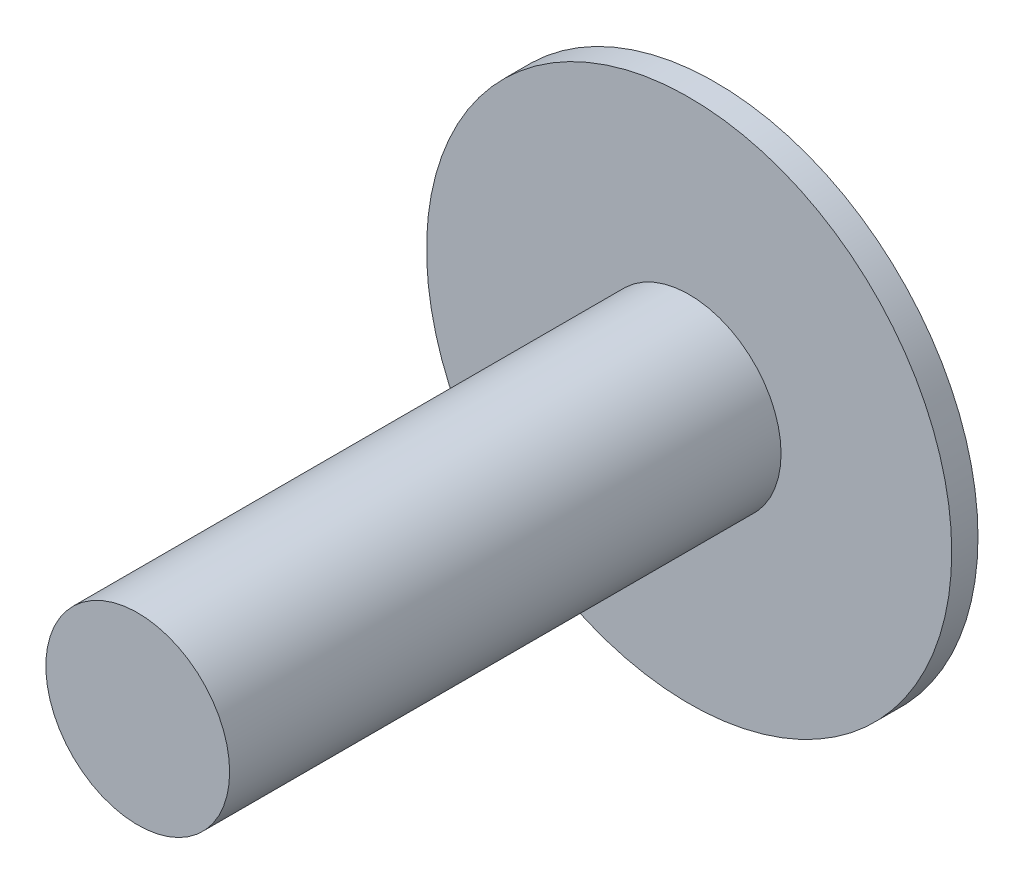
SolidWorks part; units mm, degrees
ref_plane "Alzado" through (0, 0, 0) normal (0, 0, 1) x (1, 0, 0)
ref_plane "Planta" through (0, 0, 0) normal (0, 1, 0) x (1, 0, 0)
ref_plane "Vista lateral" through (0, 0, 0) normal (1, 0, 0) x (0, 0, -1)
sketch "Croquis1" plane through (0, 0, 0) normal (0, 0, 1) x (1, 0, 0)
  circle A0 centre (0, 0) radius 10
extrude "Saliente-Extruir1" add sketch "Croquis1" along normal blind 1
sketch "Croquis2" plane through (0, 0, 1) normal (0, 0, 1) x (1, 0, 0)
  circle A0 centre (0, 0) radius 3.5
extrude "Saliente-Extruir2" add sketch "Croquis2" along normal blind 21
